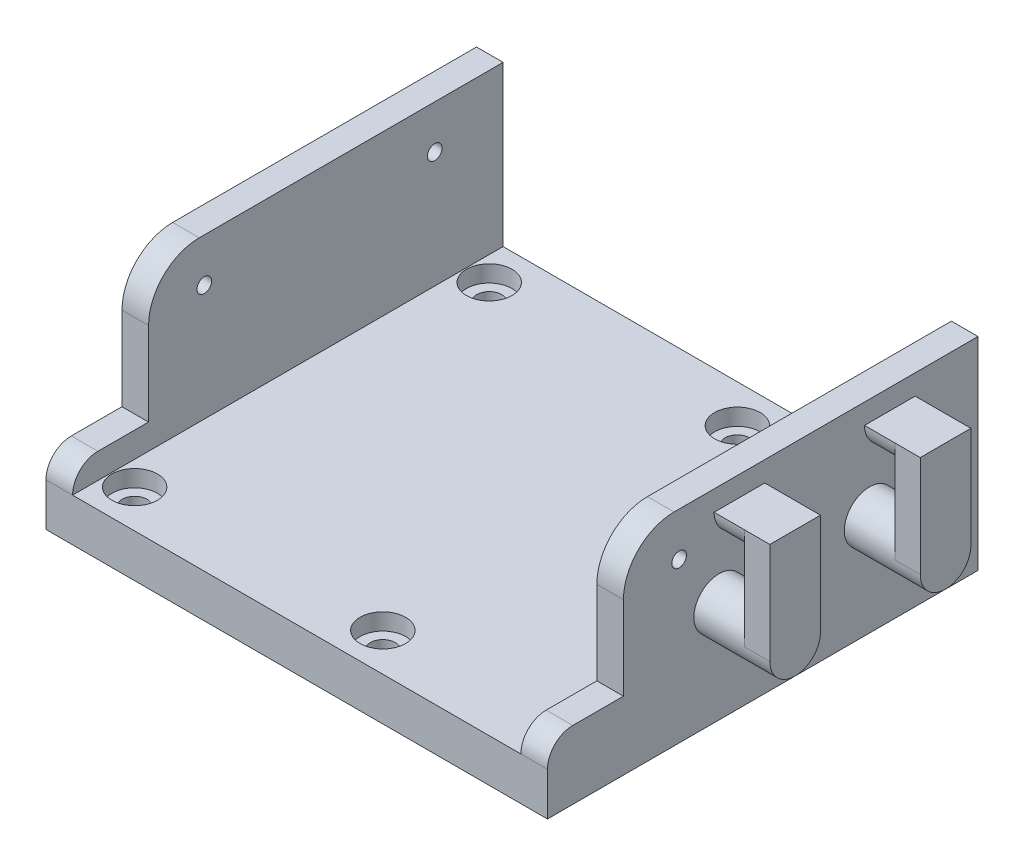
SolidWorks part; units mm, degrees
other "Markup1"
sketch "Sketch10" plane through (-60.3, 40, -50.7) normal (-0.7658, 0.6358, -0.0963) x (-0.1712, -0.0572, 0.9836)
sketch "Sketch12" plane through (-60.3, 40, -50.75) normal (-0.7658, 0.6358, -0.0963) x (-0.1712, -0.0572, 0.9836)
sketch "Sketch13" plane through (-60.3, 55, -50.75) normal (-0.7658, 0.6358, -0.0963) x (-0.1712, -0.0572, 0.9836)
sketch "Sketch14" plane through (-55.3, 55, -50.75) normal (-0.7658, 0.6358, -0.0963) x (-0.1712, -0.0572, 0.9836)
sketch "Sketch15" plane through (-49.5, 40, -42.5) normal (-0.7658, 0.6358, -0.0963) x (-0.1712, -0.0572, 0.9836)
ref_plane "Front Plane" through (0, 0, 0) normal (0, 0, 1) x (1, 0, 0)
ref_plane "Top Plane" through (0, 0, 0) normal (0, 1, 0) x (1, 0, 0)
ref_plane "Right Plane" through (0, 0, 0) normal (1, 0, 0) x (0, 0, -1)
sketch "Sketch1" plane through (0, 0, 0) normal (0, 1, 0) x (1, 0, 0)
  line L1 (-49.5, 42.5) -> (49.5, 42.5)
  line L2 (-49.5, 42.5) -> (-49.5, -42.5)
  line L3 (-49.5, -42.5) -> (49.5, -42.5)
  line L4 (49.5, 42.5) -> (49.5, -42.5)
  line L5 (-49.5, 42.5) -> (49.5, -42.5) construction
  line L6 (-49.5, -42.5) -> (49.5, 42.5) construction
  point P0 (0, 0)
  dimension "D1" = 85
  dimension "D2" = 99
extrude "Boss-Extrude1" add sketch "Sketch1" along normal blind 40 contours L2 L1 L4 L3
sketch "Sketch2" plane through (0, 40, 0) normal (0, 1, 0) x (1, 0, 0)
  line L0 (49.5, 42.5) -> (49.5, -42.5) construction
  line L1 (-44.25, -42.5) -> (44.25, -42.5)
  line L2 (-44.25, -42.5) -> (-44.25, 42.5)
  line L3 (-44.25, 42.5) -> (44.25, 42.5)
  line L4 (44.25, -42.5) -> (44.25, 42.5)
  line L5 (-44.25, -42.5) -> (44.25, 42.5) construction
  line L6 (-44.25, 42.5) -> (44.25, -42.5) construction
  line L7 (-49.5, -42.5) -> (49.5, -42.5) construction
  point P0 (0, 0)
  dimension "D1" = 5.25
  dimension "D2" = 0
extrude "Cut-Extrude1" cut sketch "Sketch2" against normal blind 31.5
sketch "Sketch5" plane through (0, 8.5, 0) normal (0, 1, 0) x (1, 0, 0)
  line L0 (-49.5, 42.5) -> (-49.5, -42.5) construction
  line L1 (-49.5, 42.5) -> (-49.5, -42.5) construction
  line L3 (-49.5, 42.5) -> (-44.25, 42.5) construction
  circle A0 centre (-39.5, 35) radius 4.5
  circle A1 centre (9.5, 35) radius 4.5
  circle A2 centre (-39.5, -35) radius 4.5
  circle A3 centre (9.5, -35) radius 4.5
  dimension "D3" = 9
  dimension "D4" = 9
  dimension "D5" = 9
  dimension "D8" = 9
  dimension "D1" = 10
  dimension "D2" = 7.5
  dimension "D6" = 70
  dimension "D7" = 49
  dimension "D9" = 10
  dimension "D10" = 70
extrude "Cut-Extrude3" cut sketch "Sketch5" against normal blind 3.3
sketch "Sketch6" plane through (0, 5.2, 0) normal (0, 1, 0) x (1, 0, 0)
  circle A0 centre (-39.5, 35) radius 2.45
  circle A1 centre (9.5, 35) radius 2.45
  circle A2 centre (9.5, -35) radius 2.45
  circle A3 centre (-39.5, -35) radius 2.45
  circle A4 centre (-39.5, -35) radius 4.5 construction
  dimension "D1" = 4.9
  dimension "D2" = 4.9
  dimension "D3" = 4.9
  dimension "D4" = 4.9
extrude "Cut-Extrude4" cut sketch "Sketch6" against normal up to surface (5.2 mm away) up to face at (0, 0, 0)
sketch "Sketch16" plane through (-49.5, 0, 0) normal (-1, 0, 0) x (0, 0, 1)
  line L3 (-42.5, 40) -> (-42.5, 0) construction
  circle A0 centre (-29, 31.4) radius 1.45
  circle A2 centre (16.5, 31.4) radius 1.45
  dimension "D3" = 2.9
  dimension "D4" = 2.9
  dimension "D1" = 13.5
  dimension "D2" = 22.9
  dimension "D5" = 45.5
extrude "Cut-Extrude6" cut sketch "Sketch16" against normal up to surface (93.75 mm away)
mirror "Mirror1" about plane through (0, 0, 0) normal (1, 0, 0) of "Cut-Extrude6"
sketch "Sketch17" plane through (49.5, 0, 0) normal (1, 0, 0) x (0, 0, -1)
  line L1 (42.5, 40) -> (-42.5, 40) construction
  circle A0 centre (-8.6, 20) radius 5
  circle A3 centre (21.1, 20) radius 5
  circle A4 centre (-16.5, 31.4) radius 1.45 construction
  circle A6 centre (29, 31.4) radius 1.45 construction
  dimension "D1" = 10
  dimension "D2" = 20
  dimension "D4" = 10
  dimension "D5" = 7.9
  dimension "D3" = 7.9
extrude "Boss-Extrude2" add sketch "Sketch17" along normal blind 15
sketch "Sketch18" plane through (64.5, 0, 0) normal (1, 0, 0) x (0, 0, -1)
  line L1 (-13.6, 20) -> (-3.6, 20)
  line L2 (-13.6, 20) -> (-13.6, 40)
  line L3 (-13.6, 40) -> (-3.6, 40)
  line L4 (-3.6, 20) -> (-3.6, 40)
  circle A0 centre (-8.6, 20) radius 5 construction
  circle A1 centre (-8.6, 20) radius 5 construction
  point P8 (-12.5, 20)
  dimension "D1" = 20
extrude "Boss-Extrude3" add sketch "Sketch18" against normal blind 5
sketch "Sketch19" plane through (64.5, 0, 0) normal (1, 0, 0) x (0, 0, -1)
  line L0 (-3.6, 40) -> (-13.6, 40) construction
  line L1 (-13.6, 40) -> (-3.6, 40)
  arc A0 (-13.6, 40) -> (-3.6, 40) centre (-8.6, 40) ccw
extrude "Boss-Extrude4" add sketch "Sketch19" against normal blind 11
sketch "Sketch20" plane through (-49.5, 0, 0) normal (-1, 0, 0) x (0, 0, 1)
  line L0 (-42.5, 40) -> (42.5, 40) construction
  line L1 (27.5, 40) -> (42.5, 40)
  line L2 (27.5, 40) -> (27.5, 13.5)
  line L3 (27.5, 13.5) -> (42.5, 13.5)
  line L4 (42.5, 40) -> (42.5, 13.5)
  line L5 (42.5, 40) -> (42.5, 0) construction
  dimension "D1" = 5
  dimension "D2" = 15
extrude "Cut-Extrude7" cut sketch "Sketch20" against normal up to surface (93.75 mm away)
fillet "Fillet1" radius 10 1 edges at (-46.875, 40, 27.5)
fillet "Fillet2" radius 5 1 edges at (-46.875, 13.5, 42.5)
mirror "Mirror3" about plane through (0, 0, 0) normal (1, 0, 0) of "Fillet2", "Fillet1", "Cut-Extrude7"
sketch "Sketch21" plane through (64.5, 0, 0) normal (1, 0, 0) x (0, 0, -1)
  line L0 (42.5, 40) -> (-17.5, 40) construction
  line L1 (16.1, 20) -> (26.1, 20)
  line L2 (16.1, 20) -> (16.1, 40)
  line L3 (16.1, 40) -> (26.1, 40)
  line L4 (26.1, 20) -> (26.1, 40)
  circle A0 centre (21.1, 20) radius 5 construction
  circle A1 centre (21.1, 20) radius 5 construction
extrude "Boss-Extrude5" add sketch "Sketch21" against normal blind 5
sketch "Sketch23" plane through (64.5, 0, 0) normal (1, 0, 0) x (0, 0, -1)
  line L0 (26.1, 40) -> (16.1, 40) construction
  line L1 (16.1, 40) -> (26.1, 40)
  arc A0 (16.1, 40) -> (26.1, 40) centre (21.1, 40) ccw
extrude "Boss-Extrude7" add sketch "Sketch23" against normal blind 11
